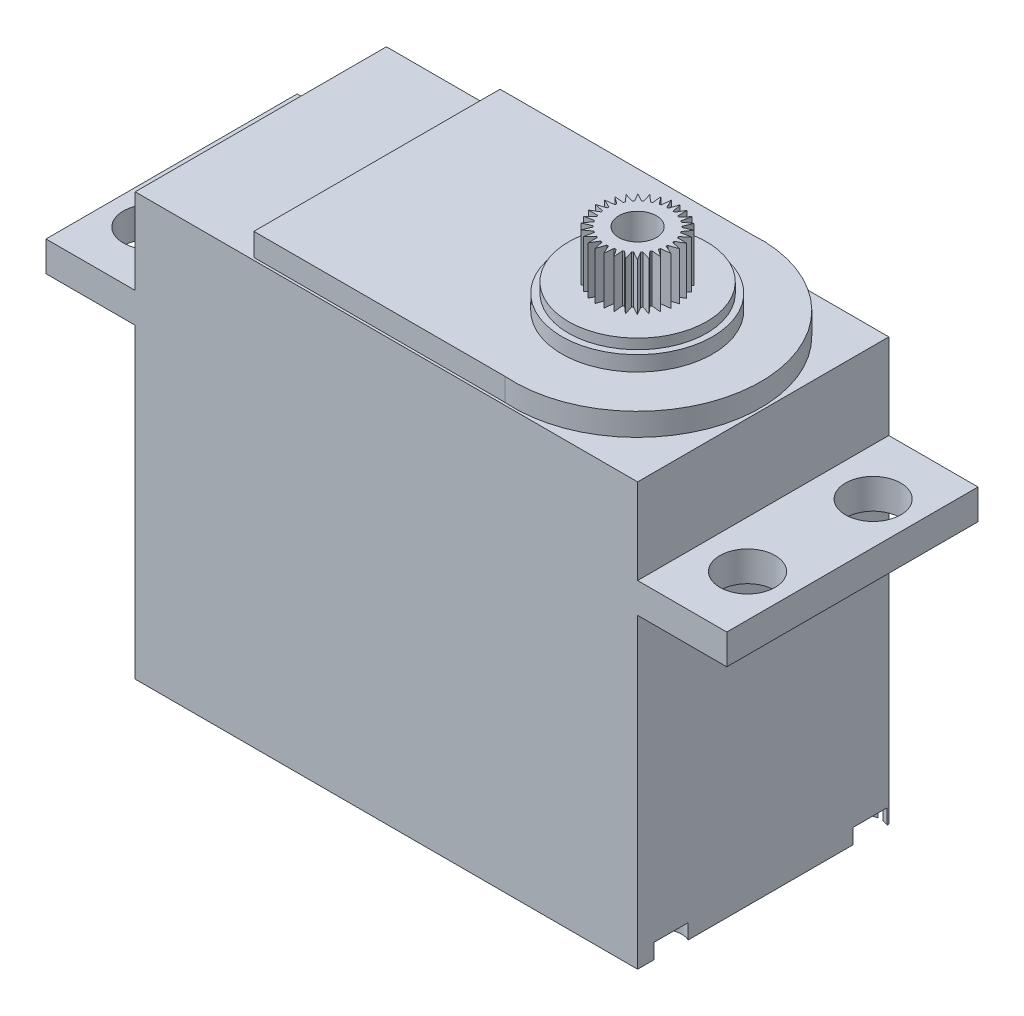
SolidWorks part; units mm, degrees
ref_plane "Front Plane" through (0, 0, 0) normal (0, 0, 1) x (1, 0, 0)
ref_plane "Top Plane" through (0, 0, 0) normal (0, 1, 0) x (1, 0, 0)
ref_plane "Right Plane" through (0, 0, 0) normal (1, 0, 0) x (0, 0, -1)
sketch "Sketch1" plane through (0, 0, 0) normal (0, 0, 1) x (1, 0, 0)
  line L1 (-24.6834, 8.2704) -> (15.3166, 8.2704)
  line L2 (-24.6834, 8.2704) -> (-24.6834, -25.3296)
  line L3 (-24.6834, -25.3296) -> (15.3166, -25.3296)
  line L4 (15.3166, 8.2704) -> (15.3166, -25.3296)
  dimension "D1" = 40
  dimension "D2" = 33.6
extrude "Boss-Extrude1" add sketch "Sketch1" along normal blind 20
sketch "Sketch2" plane through (0, 0, 20) normal (0, 0, 1) x (1, 0, 0)
  line L0 (15.3166, 8.2704) -> (15.3166, 1.4704) construction
  line L1 (15.3166, -25.3296) -> (15.3166, 8.2704) construction
  line L2 (-4.6834, 8.2704) -> (-4.6834, -3.6681) construction
  line L3 (15.3166, 1.4704) -> (22.4166, 1.4704)
  line L4 (15.3166, 1.4704) -> (15.3166, -0.9296)
  line L5 (15.3166, -0.9296) -> (22.4166, -0.9296)
  line L6 (22.4166, 1.4704) -> (22.4166, -0.9296)
  line L7 (15.3166, 8.2704) -> (-24.6834, 8.2704) construction
  line L8 (-31.7834, 1.4704) -> (-31.7834, -0.9296)
  line L9 (-24.6834, 1.4704) -> (-24.6834, -0.9296)
  line L10 (-24.6834, -0.9296) -> (-31.7834, -0.9296)
  line L11 (-24.6834, 1.4704) -> (-31.7834, 1.4704)
  dimension "D1" = 6.8
  dimension "D2" = 2.4
  dimension "D3" = 7.1
extrude "Boss-Extrude2" add sketch "Sketch2" against normal blind 20
ref_plane "Plane1" through (0, 0, 10.5) normal (0, 0, 1) x (1, 0, 0)
sketch "Sketch4" plane through (0, 1.4704, 0) normal (0, 1, 0) x (1, 0, 0)
  line L0 (19.0666, -15) -> (19.0666, -20) construction
  line L1 (19.0666, -5) -> (19.0666, 0) construction
  line L2 (22.4166, 0) -> (15.3166, 0) construction
  line L3 (15.3166, -15) -> (19.0666, -15) construction
  line L4 (15.3166, -20) -> (15.3166, 0) construction
  line L5 (15.3166, -5) -> (19.0666, -5) construction
  line L6 (-4.6834, 0) -> (-4.6834, -4.967) construction
  line L7 (15.3166, 0) -> (-24.6834, 0) construction
  line L8 (15.3166, 0) -> (15.3166, -20) construction
  line L11 (22.4166, -20) -> (15.3166, -20) construction
  circle A0 centre (19.0666, -15) radius 2.2
  circle A1 centre (19.0666, -5) radius 2.2
  circle A2 centre (-28.4334, -15) radius 2.2
  circle A3 centre (-28.4334, -5) radius 2.2
  point P20 (0, 0)
  point P21 (0, 0)
  point P22 (0, 0)
  point P25 (21.6137, -5.8255)
  point P26 (0, 0)
  point P29 (0, 0)
  dimension "D2" = 4.4
  dimension "D3" = 4.4
  dimension "D4" = 3.75
  dimension "D1" = 5
  dimension "D5" = 47.5
  dimension "D6" = 5
  dimension "D7" = 10
  dimension "D8" = 3.75
extrude "Cut-Extrude1" cut sketch "Sketch4" against normal blind 3
sketch "Sketch5" plane through (0, 8.2704, 0) normal (0, 1, 0) x (1, 0, 0)
  line L0 (15.3166, -20) -> (-24.6834, -20) construction
  line L4 (-15.4334, -0.2) -> (-15.4334, -19.8)
  line L5 (-15.4334, -19.8) -> (4.5666, -19.8)
  line L6 (4.5666, -0.2) -> (-15.4334, -0.2)
  line L7 (-24.6834, -20) -> (-24.6834, 0) construction
  line L8 (15.3166, 0) -> (-24.6834, 0) construction
  arc A1 (4.5666, -0.2) -> (4.5666, -19.8) centre (5.2883, -10) cw
  dimension "D1" = 0.2
  dimension "D2" = 0.2
  dimension "D3" = 9.25
  dimension "D4" = 20
extrude "Boss-Extrude4" add sketch "Sketch5" along normal blind 1.8
sketch "Sketch6" plane through (0, -25.3296, 0) normal (0, -1, 0) x (1, 0, 0)
  circle A0 centre (-22.6606, 17.3297) radius 1.5
  circle A1 centre (-22.6606, 1.4871) radius 1.5
  circle A2 centre (14.6705, 17.3297) radius 1.5
  circle A3 centre (14.6705, 1.4871) radius 1.5
  dimension "D1" = 3
extrude "Cut-Extrude2" cut sketch "Sketch6" against normal blind 1.2
sketch "Sketch7" plane through (0, 10.0704, 0) normal (0, 1, 0) x (1, 0, 0)
  line L0 (15.1148, -10) -> (5.2883, -10) construction
  arc A0 (4.5666, -19.8) -> (4.5666, -0.2) centre (5.2883, -10) ccw construction
  circle A1 centre (5.2883, -10) radius 6
  dimension "D1" = 12
extrude "Boss-Extrude5" add sketch "Sketch7" along normal blind 1.2
sketch "Sketch8" plane through (0, 11.2704, 0) normal (0, 1, 0) x (1, 0, 0)
  line L0 (15.3166, 0) -> (-24.6834, 0) construction
  line L1 (15.3166, -20) -> (15.3166, 0) construction
  circle A0 centre (5.3166, -10) radius 5.5
  point P2 (0, 0)
  point P5 (0, 0)
  dimension "D1" = 11
  dimension "D2" = 10
  dimension "D3" = 10
extrude "Boss-Extrude6" add sketch "Sketch8" along normal blind 0.8
sketch "Sketch10" plane through (0, 12.0704, 0) normal (0, 1, 0) x (1, 0, 0)
  circle A0 centre (5.3166, -10) radius 2.5
  dimension "D1" = 5
extrude "Boss-Extrude8" add sketch "Sketch10" along normal blind 3.8
sketch "Sketch11" plane through (0, 15.8704, 0) normal (0, 1, 0) x (1, 0, 0)
  line L0 (5.5034, -6.8019) -> (5.2719, -7.5004)
  line L1 (5.2719, -7.5004) -> (5.6647, -7.5244)
  line L2 (5.6647, -7.5244) -> (5.5034, -6.8019)
  circle A0 centre (5.3166, -10) radius 2.5 construction
extrude "Boss-Extrude9" add sketch "Sketch11" against normal blind 4
pattern_circular "CirPattern2" count 30 over 360 about axis through (5.3166, 0, 10) along (0, 1, 0) of "Boss-Extrude9"
sketch "Sketch12" plane through (0, 15.8704, 0) normal (0, 1, 0) x (1, 0, 0)
  circle A0 centre (5.3166, -10) radius 1.5
  dimension "D1" = 3
extrude "Cut-Extrude4" cut sketch "Sketch12" against normal blind 4
